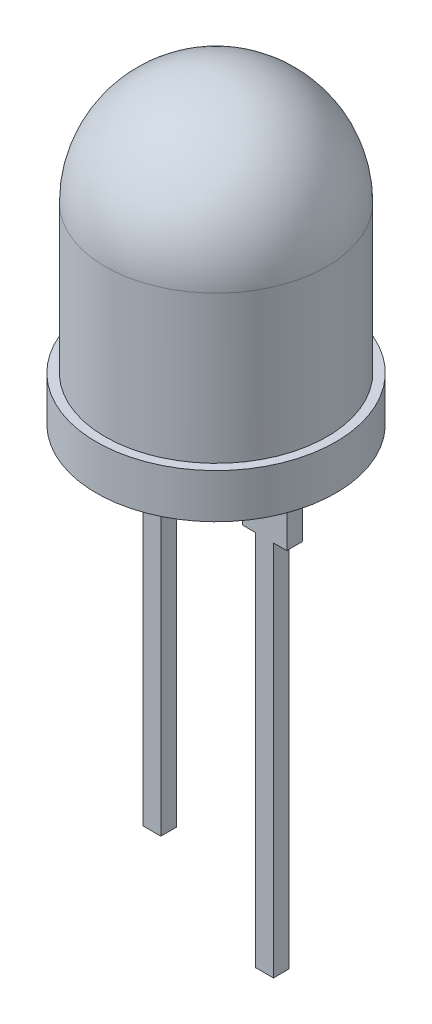
SolidWorks part; units mm, degrees
ref_plane "Front Plane" through (0, 0, 0) normal (0, 0, 1) x (1, 0, 0)
ref_plane "Top Plane" through (0, 0, 0) normal (0, 1, 0) x (1, 0, 0)
ref_plane "Right Plane" through (0, 0, 0) normal (1, 0, 0) x (0, 0, -1)
sketch "Sketch1" plane through (0, 0, 0) normal (0, 0, 1) x (1, 0, 0)
  line L0 (0, 0) -> (0, 74.7763) construction
  line L1 (0, 0) -> (5.4, 0)
  line L2 (5.4, 0) -> (5.4, 2)
  line L3 (5.4, 2) -> (5, 2)
  line L4 (5, 2) -> (5, 8.65)
  line L5 (0, 13.65) -> (0, 0)
  arc A0 (5, 8.65) -> (0, 13.65) centre (0, 8.65) ccw
  dimension "D1" = 10.8
  dimension "D2" = 10
  dimension "D3" = 2
  dimension "D4" = 13.65
revolve "Revolve1" add sketch "Sketch1" angle 360 about L0
sketch "Sketch3" plane through (0, 0, 0) normal (0, 0, 1) x (1, 0, 0)
  line L0 (0, 0) -> (0, -9.7387) construction
  line L1 (-5.4, 0) -> (5.4, 0) construction
  line L2 (1.54, -3) -> (1.54, 0)
  line L3 (2.14, -3) -> (1.54, -3)
  line L4 (2.14, -3) -> (2.14, -20)
  line L5 (2.94, -3) -> (2.94, -20)
  line L6 (2.94, -3) -> (3.54, -3)
  line L7 (3.54, -3) -> (3.54, 0)
  line L8 (3.54, 0) -> (1.54, 0)
  line L9 (2.54, 0) -> (2.54, -6.772) construction
  line L10 (2.14, -20) -> (2.94, -20)
  line L11 (-2.54, 0) -> (-2.54, -6.772) construction
  line L12 (-2.14, -17) -> (-2.94, -17)
  line L13 (-3.54, 0) -> (-1.54, 0)
  line L14 (-3.54, -3) -> (-3.54, 0)
  line L15 (-2.94, -3) -> (-3.54, -3)
  line L16 (-2.94, -3) -> (-2.94, -17)
  line L17 (-2.14, -3) -> (-2.14, -17)
  line L18 (-2.14, -3) -> (-1.54, -3)
  line L19 (-1.54, -3) -> (-1.54, 0)
  dimension "D1" = 2
  dimension "D2" = 0.8
  dimension "D3" = 2.54
  dimension "D4" = 3
  dimension "D5" = 20
  dimension "D6" = 17
extrude "Boss-Extrude1" add sketch "Sketch3" along normal mid plane 0.7
